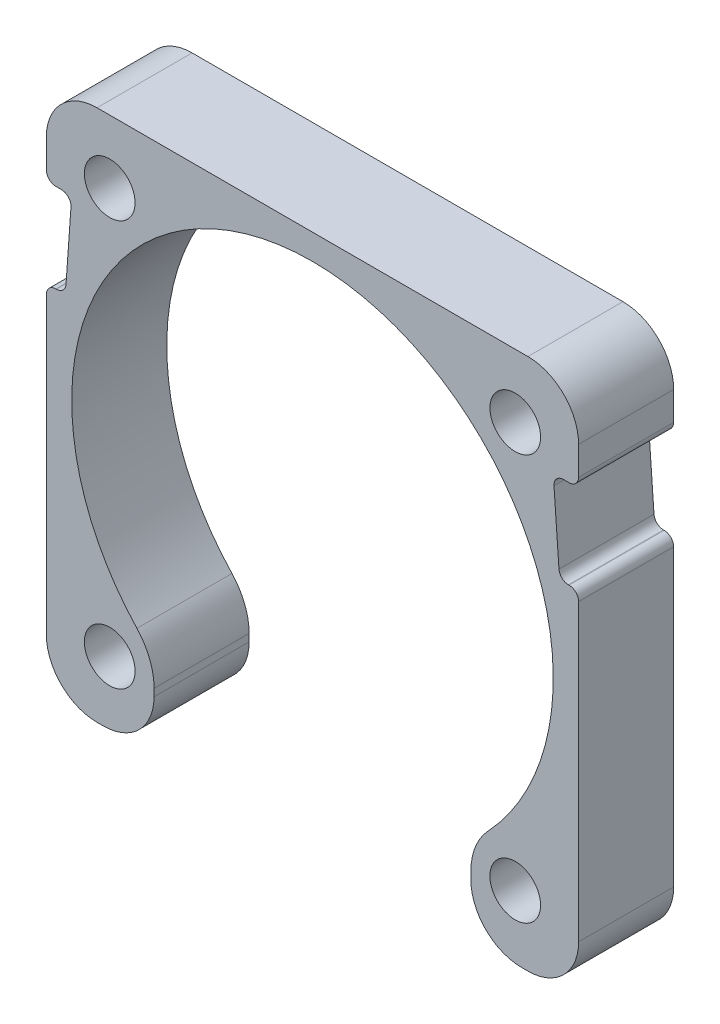
SolidWorks part; units mm, degrees
material "ABS"
ref_plane "Alzado" through (0, 0, 0) normal (0, 0, 1) x (1, 0, 0)
ref_plane "Planta" through (0, 0, 0) normal (0, 1, 0) x (1, 0, 0)
ref_plane "Vista lateral" through (0, 0, 0) normal (1, 0, 0) x (0, 0, -1)
sketch "Croquis1" plane through (0, 0, 0) normal (0, 0, 1) x (1, 0, 0)
  line L1 (21, -21) -> (-21, -21)
  line L2 (21, -21) -> (21, 21)
  line L3 (21, 21) -> (-21, 21)
  line L4 (-21, -21) -> (-21, 21)
  line L5 (21, -21) -> (-21, 21) construction
  line L6 (21, 21) -> (-21, -21) construction
  point P0 (0, 0)
  dimension "D1" = 42
extrude "Saliente-Extruir1" add sketch "Croquis1" along normal blind 7.5
sketch "Croquis2" plane through (0, 0, 7.5) normal (0, 0, 1) x (1, 0, 0)
  circle A0 centre (0, 0) radius 19
  dimension "D1" = 38
extrude "Cortar-Extruir1" cut sketch "Croquis2" against normal through all
sketch "Croquis3" plane through (0, 0, 7.5) normal (0, 0, 1) x (1, 0, 0)
  line L1 (16, -16) -> (-16, -16) construction
  line L2 (16, -16) -> (16, 16) construction
  line L3 (16, 16) -> (-16, 16) construction
  line L4 (-16, -16) -> (-16, 16) construction
  line L5 (16, -16) -> (-16, 16) construction
  line L6 (16, 16) -> (-16, -16) construction
  circle A0 centre (-16, 16) radius 2
  circle A1 centre (16, 16) radius 2
  circle A2 centre (16, -16) radius 2
  circle A3 centre (-16, -16) radius 2
  point P0 (0, 0)
  dimension "D2" = 4
  dimension "D1" = 32
extrude "Cortar-Extruir2" cut sketch "Croquis3" against normal through all
sketch "Croquis4" plane through (0, 0, 7.5) normal (0, 0, 1) x (1, 0, 0)
  line L0 (-21, -21) -> (21, -21) construction
  line L1 (-12.5, 12.5) -> (12.5, 12.5)
  line L2 (-12.5, 12.5) -> (-12.5, -21)
  line L3 (-12.5, -21) -> (12.5, -21)
  line L4 (12.5, 12.5) -> (12.5, -21)
  line L6 (0, 0) -> (0, -21) construction
  circle A2 centre (-16, -16) radius 2 construction
  circle A3 centre (16, 16) radius 2 construction
  dimension "D2" = 3.5
  dimension "D1" = 3.5
extrude "Cortar-Extruir3" cut sketch "Croquis4" against normal through all
fillet "Redondeo1" radius 4 6 edges at (-21, -21, 3.75) (21, -21, 3.75) (21, 21, 3.75) (-21, 21, 3.75) (12.5, -21, 3.75) (-12.5, -21, 3.75)
fillet "Redondeo2" radius 5 2 edges at (12.5, -14.3091, 3.75) (-12.5, -14.3091, 3.75)
sketch "Croquis5" plane through (0, 0, 7.5) normal (0, 0, 1) x (1, 0, 0)
  line L1 (17, 21) -> (-17, 21) construction
  line L3 (21, -17) -> (21, 17) construction
  line L5 (-16, 16) -> (0, 0) construction
  line L10 (0, 0) -> (0, 34.9729) construction
  line L15 (-21, 7) -> (-21, 14)
  line L16 (-21, 7) -> (-19.5, 7)
  line L17 (-19.5, 7) -> (-19, 14)
  line L18 (-21, 14) -> (-19, 14)
  line L19 (21, 14) -> (19, 14)
  line L20 (19.5, 7) -> (19, 14)
  line L21 (21, 7) -> (19.5, 7)
  line L22 (21, 7) -> (21, 14)
  dimension "D1" = 7
  dimension "D2" = 7
  dimension "D3" = 2
  dimension "D4" = 1.5
extrude "Cortar-Extruir4" cut sketch "Croquis5" against normal through all
fillet "Redondeo3" radius 0.75 8 edges at (-21, 7, 3.75) (-19.5, 7, 3.75) (-19, 14, 3.75) (-21, 14, 3.75) (21, 7, 3.75) (19.5, 7, 3.75) (19, 14, 3.75) (21, 14, 3.75)
